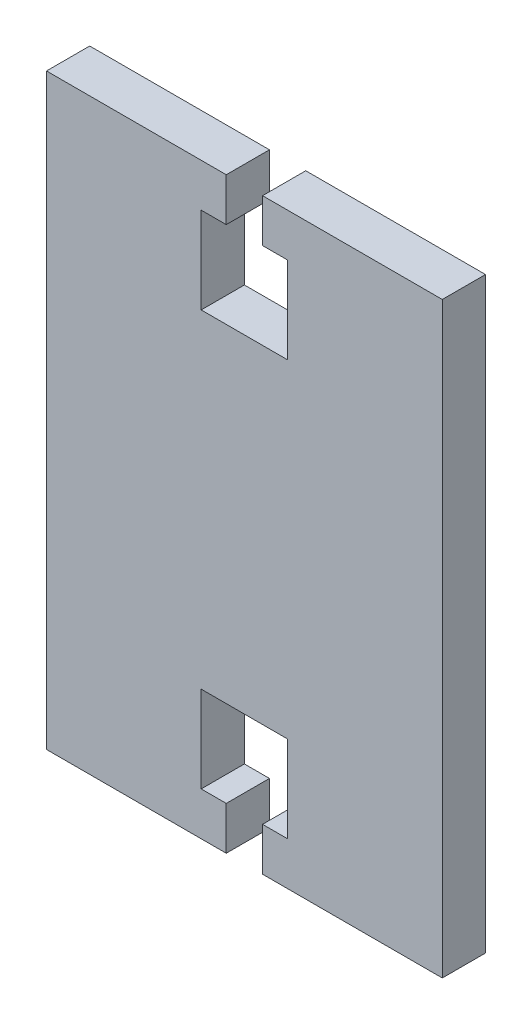
SolidWorks part; units mm, degrees
ref_plane "Front Plane" through (0, 0, 0) normal (0, 0, 1) x (1, 0, 0)
ref_plane "Top Plane" through (0, 0, 0) normal (0, 1, 0) x (1, 0, 0)
ref_plane "Right Plane" through (0, 0, 0) normal (1, 0, 0) x (0, 0, -1)
sketch "Sketch1" plane through (0, 0, 0) normal (0, 0, 1) x (1, 0, 0)
  line L1 (22.9, -34) -> (-22.9, -34)
  line L2 (22.9, -34) -> (22.9, 34)
  line L3 (22.9, 34) -> (-22.9, 34)
  line L4 (-22.9, -34) -> (-22.9, 34)
  line L5 (22.9, -34) -> (-22.9, 34) construction
  line L6 (22.9, 34) -> (-22.9, -34) construction
  point P0 (0, 0)
  dimension "D1" = 68
  dimension "D2" = 45.8
extrude "Boss-Extrude1" add sketch "Sketch1" along normal blind 5
sketch "Sketch2" plane through (0, 0, 5) normal (0, 0, 1) x (1, 0, 0)
  line L0 (0, 34) -> (0, 17.2771) construction
  line L1 (22.9, 34) -> (-22.9, 34) construction
  line L2 (22.9, 0) -> (-5.3314, 0) construction
  line L3 (22.9, -34) -> (22.9, 34) construction
  line L4 (-2.1, 34) -> (2.1, 34)
  line L5 (2.1, 34) -> (2.1, 29)
  line L6 (2.1, 29) -> (5, 29)
  line L7 (5, 29) -> (5, 19)
  line L8 (5, 19) -> (-5, 19)
  line L9 (-5, 29) -> (-5, 19)
  line L10 (-2.1, 29) -> (-5, 29)
  line L11 (-2.1, 34) -> (-2.1, 29)
  line L12 (0, -34) -> (0, -17.2771) construction
  line L13 (-2.1, -34) -> (-2.1, -29)
  line L14 (-2.1, -29) -> (-5, -29)
  line L15 (-5, -29) -> (-5, -19)
  line L16 (5, -19) -> (-5, -19)
  line L17 (5, -29) -> (5, -19)
  line L18 (2.1, -29) -> (5, -29)
  line L19 (2.1, -34) -> (2.1, -29)
  line L20 (-2.1, -34) -> (2.1, -34)
  point P15 (0, 19)
  point P28 (0, -19)
  dimension "D1" = 2.1
  dimension "D2" = 5
  dimension "D3" = 10
  dimension "D4" = 5
extrude "Cut-Extrude1" cut sketch "Sketch2" against normal blind 5
